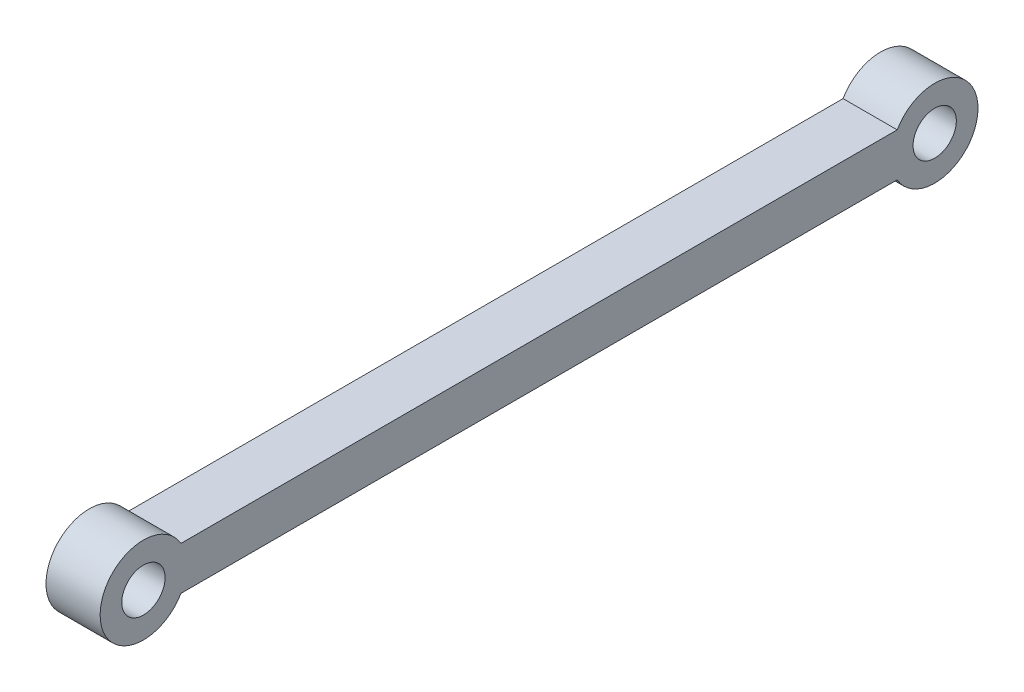
SolidWorks part; units mm, degrees
ref_plane "Front Plane" through (0, 0, 0) normal (0, 0, 1) x (1, 0, 0)
ref_plane "Top Plane" through (0, 0, 0) normal (0, 1, 0) x (1, 0, 0)
ref_plane "Right Plane" through (0, 0, 0) normal (1, 0, 0) x (0, 0, -1)
sketch "Sketch1" plane through (0, 0, 0) normal (1, 0, 0) x (0, 0, -1)
  line L0 (-16.541, 1) -> (16.541, 1)
  line L5 (-16.541, -1) -> (16.541, -1)
  line L6 (0, 1) -> (0, -1) construction
  circle A1 centre (-18.2731, 0) radius 1
  arc A2 (-16.541, 1) -> (-16.541, -1) centre (-18.2731, 0) ccw
  circle A4 centre (18.2731, 0) radius 1
  arc A5 (16.541, -1) -> (16.541, 1) centre (18.2731, 0) ccw
  point P0 (0, 0)
  point P11 (0, 1)
  point P13 (0, -1)
  point P16 (0, 0)
  dimension "D1" = 2
  dimension "D2" = 4
  dimension "D3" = 36.5461
  dimension "D4" = 2
extrude "Boss-Extrude1" add sketch "Sketch1" along normal mid plane 2.5
